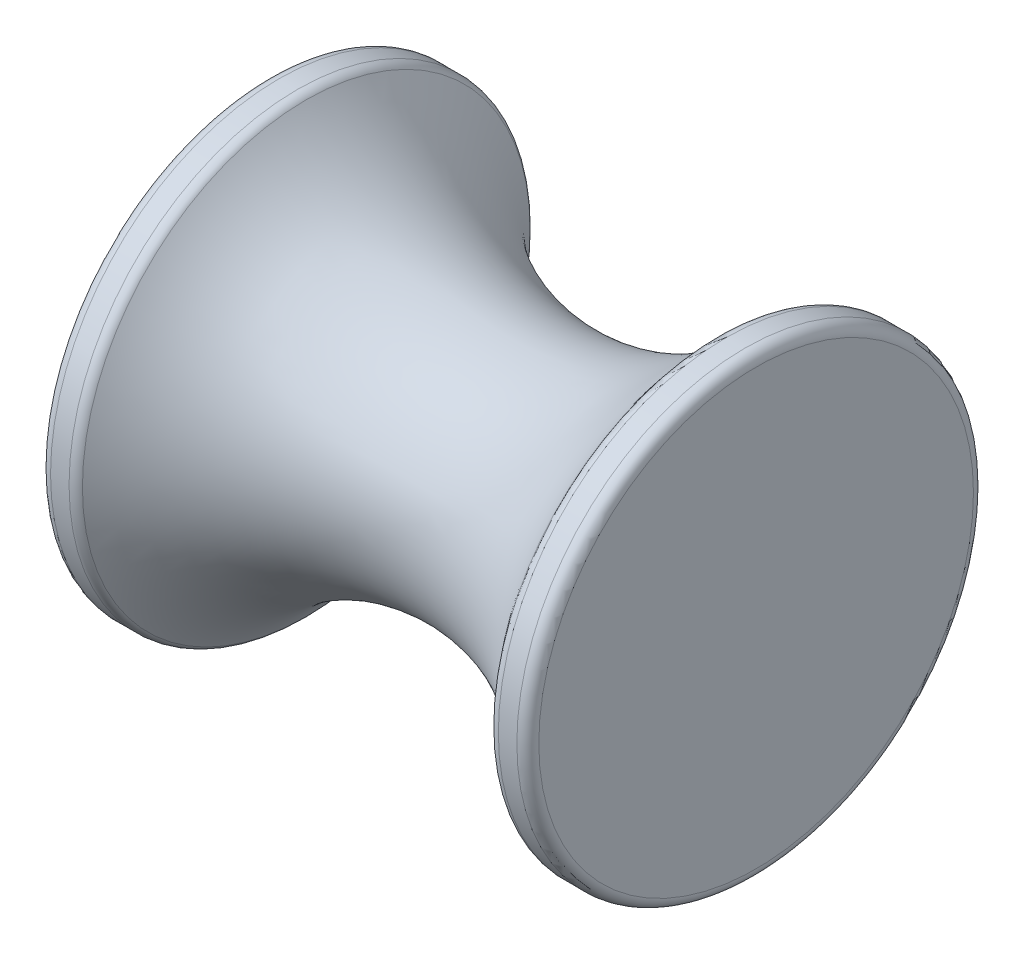
SolidWorks part; units mm, degrees
ref_plane "Front" through (0, 0, 0) normal (0, 0, 1) x (1, 0, 0)
ref_plane "Top" through (0, 0, 0) normal (0, 1, 0) x (1, 0, 0)
ref_plane "Right" through (0, 0, 0) normal (1, 0, 0) x (0, 0, -1)
sketch "Sketch1" plane through (0, 0, 0) normal (0, 0, 1) x (1, 0, 0)
  line L0 (-17.653, 0) -> (17.653, 0)
  line L1 (17.653, 0) -> (17.653, 16.51)
  line L2 (17.653, 16.51) -> (15.113, 16.51)
  line L3 (-17.653, 0) -> (-17.653, 16.51)
  line L4 (-17.653, 16.51) -> (-15.113, 16.51)
  line L5 (0, 0) -> (0, 8.636) construction
  line L6 (17.653, 10.414) -> (15.367, 10.414)
  line L7 (15.367, 10.414) -> (15.367, 6.35)
  line L8 (15.367, 6.35) -> (10.541, 6.35)
  line L9 (9.017, 3.81) -> (10.541, 4.826)
  line L10 (9.017, 3.81) -> (-9.017, 3.81)
  line L11 (-9.017, 3.81) -> (-10.541, 4.826)
  line L12 (-10.541, 6.35) -> (-15.367, 6.35)
  line L13 (-15.367, 6.35) -> (-15.367, 10.414)
  line L14 (-15.367, 10.414) -> (-17.653, 10.414)
  line L15 (10.541, 6.35) -> (10.541, 4.826)
  line L16 (-10.541, 6.35) -> (-10.541, 4.826)
  line L17 (-17.653, 16.51) -> (17.653, 0) construction
  line L18 (17.653, 16.51) -> (-17.653, 0) construction
  arc A0 (-15.113, 16.51) -> (15.113, 16.51) centre (0, 27.0766) ccw
  circle A2 centre (0, 28.1074) radius 19.05
  point P3 (0, 8.255)
  point P4 (0, 0)
  point P20 (0, 8.636)
  dimension "D12" = 18.4406
  dimension "D13" = 38.1
  dimension "D1" = 35.306
  dimension "D2" = 10.414
  dimension "D3" = 6.35
  dimension "D4" = 3.81
  dimension "D5" = 2.286
  dimension "D6" = 4.826
  dimension "D7" = 7.112
  dimension "D8" = 8.636
  dimension "D9" = 2.54
  dimension "D10" = 16.51
  dimension "D11" = 8.636
revolve "Revolve1" add sketch "Sketch1" angle 360 about L0
fillet "Fillet2" radius 0.7937 4 edges at (17.653, 0, 16.51) (15.113, 0, 16.51) (-17.653, 0, 16.51) (-15.113, 0, 16.51)
